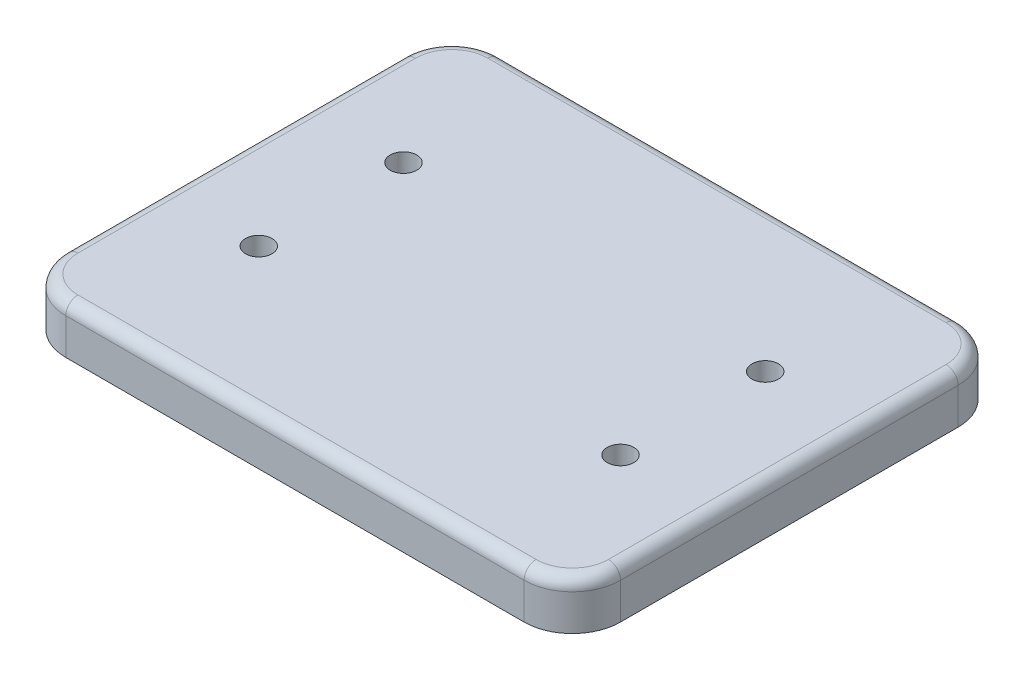
SolidWorks part; units mm, degrees
ref_plane "Front Plane" through (0, 0, 0) normal (0, 0, 1) x (1, 0, 0)
ref_plane "Top Plane" through (0, 0, 0) normal (0, 1, 0) x (1, 0, 0)
ref_plane "Right Plane" through (0, 0, 0) normal (1, 0, 0) x (0, 0, -1)
sketch "Sketch1" plane through (0, 0, 0) normal (0, 1, 0) x (1, 0, 0)
  line L1 (-95, -90) -> (95, -90)
  line L2 (-115, -70) -> (-115, 70)
  line L3 (-95, 90) -> (95, 90)
  line L4 (115, -70) -> (115, 70)
  line L5 (-115, -90) -> (115, 90) construction
  line L6 (-115, 90) -> (115, -90) construction
  arc A0 (95, -90) -> (115, -70) centre (95, -70) ccw
  arc A1 (-115, 70) -> (-95, 90) centre (-95, 70) cw
  arc A2 (-95, -90) -> (-115, -70) centre (-95, -70) cw
  arc A3 (95, 90) -> (115, 70) centre (95, 70) cw
  point P0 (0, 0)
  dimension "D3" = 20
  dimension "D1" = 230
  dimension "D2" = 180
extrude "Boss-Extrude1" add sketch "Sketch1" along normal blind 20
fillet "Fillet1" radius 5 8 edges at (0, 20, 90) (-109.1421, 20, 84.1421) (-115, 20, 0) (-109.1421, 20, -84.1421) (0, 20, -90) (109.1421, 20, -84.1421) (115, 20, 0) (109.1421, 20, 84.1421)
sketch "Sketch2" plane through (0, 20, 0) normal (0, 1, 0) x (1, 0, 0)
  circle A0 centre (-75, 30) radius 5.5
  circle A1 centre (75, 30) radius 5.5
  point P7 (-59.3279, 24.5171)
  dimension "D4" = 11
  dimension "D1" = 30
  dimension "D2" = 75
  dimension "D3" = 75
extrude "Cut-Extrude1" cut sketch "Sketch2" against normal through all
sketch "Sketch4" plane through (0, 0, 0) normal (0, -1, 0) x (1, 0, 0)
  circle A0 centre (-75, -30) radius 9
  circle A1 centre (75, -30) radius 9
  dimension "D1" = 18
extrude "Cut-Extrude2" cut sketch "Sketch4" against normal blind 11
mirror "Mirror1" about plane through (0, 0, 0) normal (0, 0, 1) of "Cut-Extrude1", "Cut-Extrude2"
